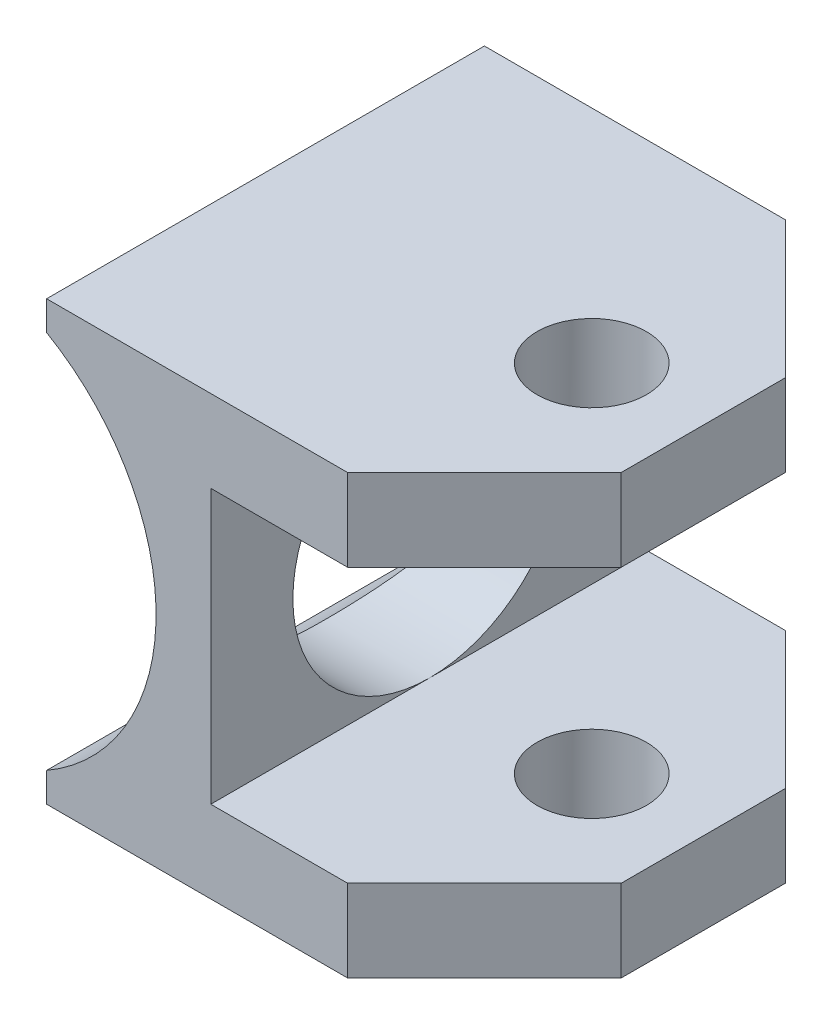
SolidWorks part; units mm, degrees
ref_plane "Front" through (0, 0, 0) normal (0, 0, 1) x (1, 0, 0)
ref_plane "Top" through (0, 0, 0) normal (0, 1, 0) x (1, 0, 0)
ref_plane "Right" through (0, 0, 0) normal (1, 0, 0) x (0, 0, -1)
sketch "Sketch1" plane through (0, 0, 0) normal (0, 0, 1) x (1, 0, 0)
  line L0 (6.35, 12.7) -> (31.75, 12.7)
  line L1 (31.75, 12.7) -> (31.75, 7.9375)
  line L2 (31.75, 7.9375) -> (15.875, 7.9375)
  line L3 (15.875, 7.9375) -> (15.875, -7.9375)
  line L4 (0, 0) -> (31.75, 0) construction
  line L5 (25.4, 12.7) -> (25.4, 0) construction
  line L6 (6.35, 12.7) -> (6.35, 10.9985)
  line L7 (31.75, -7.9375) -> (15.875, -7.9375)
  line L8 (31.75, -12.7) -> (31.75, -7.9375)
  line L9 (6.35, -12.7) -> (31.75, -12.7)
  line L10 (6.35, -12.7) -> (6.35, -10.9985)
  arc A0 (6.35, -10.9985) -> (6.35, 10.9985) centre (0, 0) ccw
  point P5 (12.7, 0)
  point P12 (15.875, 0)
  point P19 (0, 0)
  dimension "D1" = 25.4
  dimension "D2" = 7.9375
  dimension "D3" = 25.4
  dimension "D4" = 3.175
  dimension "D5" = 6.35
  dimension "D6" = 6.35
extrude "Boss-Extrude1" add sketch "Sketch1" along normal blind 25.4
hole_wizard "1/4 (0.25) Diameter Hole1" positions "Sketch2" profile "Sketch4" hole size "1/4" standard "ANSI Inch" end condition through all
sketch "Sketch2" plane through (0, 12.7, 0) normal (0, 1, 0) x (1, 0, 0)
  point P0 (25.4, -12.8218)
sketch "Sketch4" plane through (25.4, 12.7, 12.8218) normal (1, 0, 0) x (0, 0, 1)
  line L0 (0, 0) -> (0, 25.4)
  line L1 (0, 25.4) -> (3.175, 25.4)
  line L2 (3.175, 25.4) -> (3.175, 0)
  line L5 (3.175, 0) -> (0, 0)
  line L11 (0, -6.35) -> (0, 107.95) construction
  dimension "Thru Hole Dia." = 6.35
  dimension "Thru Hole Depth" = 25.4
chamfer "Chamfer1" distance 7.9375 angle 45 4 edges at (31.75, 10.3188, 0) (31.75, -10.3188, 0) (31.75, -10.3188, 25.4) (31.75, 10.3188, 25.4)
sketch3d "3DSketch1"
  line L0 (25.4, 12.7, 12.8218) -> (25.4, -12.7, 12.8218)
  line L1 (25.4, 0, 12.8218) -> (0, 0, 12.8218)
  circle A0 centre (25.4, 12.7, 12.8218) radius 3.175 construction
  circle A1 centre (25.4, -12.7, 12.8218) radius 3.175 construction
  point P3 (25.4, 0, 12.8218)
  point P6 (25.4, 15.875, 12.8218)
  point P9 (25.4, -9.525, 12.8218)
sketch "Sketch6" plane through (15.875, 0, 0) normal (1, 0, 0) x (0, 0, -1)
  line L0 (-25.4, 0) -> (0, 0) construction
  line L1 (-25.4, -7.9375) -> (-25.4, 7.9375) construction
  circle A0 centre (-12.7, 0) radius 7.9375
  dimension "D1" = 15.875
extrude "Cut-Extrude1" cut sketch "Sketch6" against normal through all
move or copy body "Body-Move/Copy1" [suppressed] bodies to move or copy 104
move or copy body "Body-Move/Copy2" [suppressed] bodies to move or copy 104
equation "\"D2@Sketch1\"=(.375)/2+.125"
